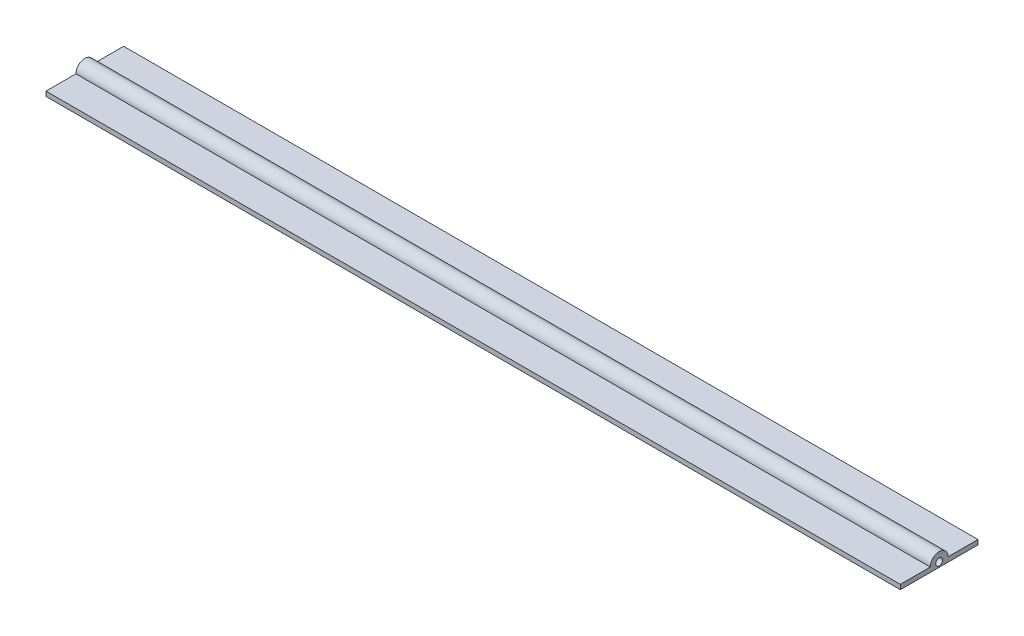
SolidWorks part; units mm, degrees
ref_plane "Front" through (0, 0, 0) normal (0, 0, 1) x (1, 0, 0)
ref_plane "Top" through (0, 0, 0) normal (0, 1, 0) x (1, 0, 0)
ref_plane "Right" through (0, 0, 0) normal (1, 0, 0) x (0, 0, -1)
sketch "Sketch1" plane through (0, 0, 0) normal (1, 0, 0) x (0, 0, -1)
  line L0 (15.6124, 1.524) -> (25.4, 1.524)
  line L1 (0, 0) -> (25.4, 0)
  line L2 (0, 0) -> (0, 1.524)
  line L3 (0, 1.524) -> (9.7876, 1.524)
  line L4 (25.4, 0) -> (25.4, 1.524)
  line L5 (0, 0) -> (25.4, 1.524) construction
  line L6 (0, 1.524) -> (25.4, 0) construction
  arc A1 (15.6124, 1.524) -> (9.7876, 1.524) centre (12.7, 1.524) ccw
  point P4 (12.7, 0.762)
  dimension "D1" = 1.524
  dimension "D2" = 25.4
extrude "Boss-Extrude1" add sketch "Sketch1" along normal blind 279.4
sketch "Sketch2" plane through (279.4, 0, 0) normal (1, 0, 0) x (0, 0, -1)
  circle A0 centre (12.7, 1.524) radius 1.1256
extrude "Cut-Extrude1" cut sketch "Sketch2" against normal up to next
